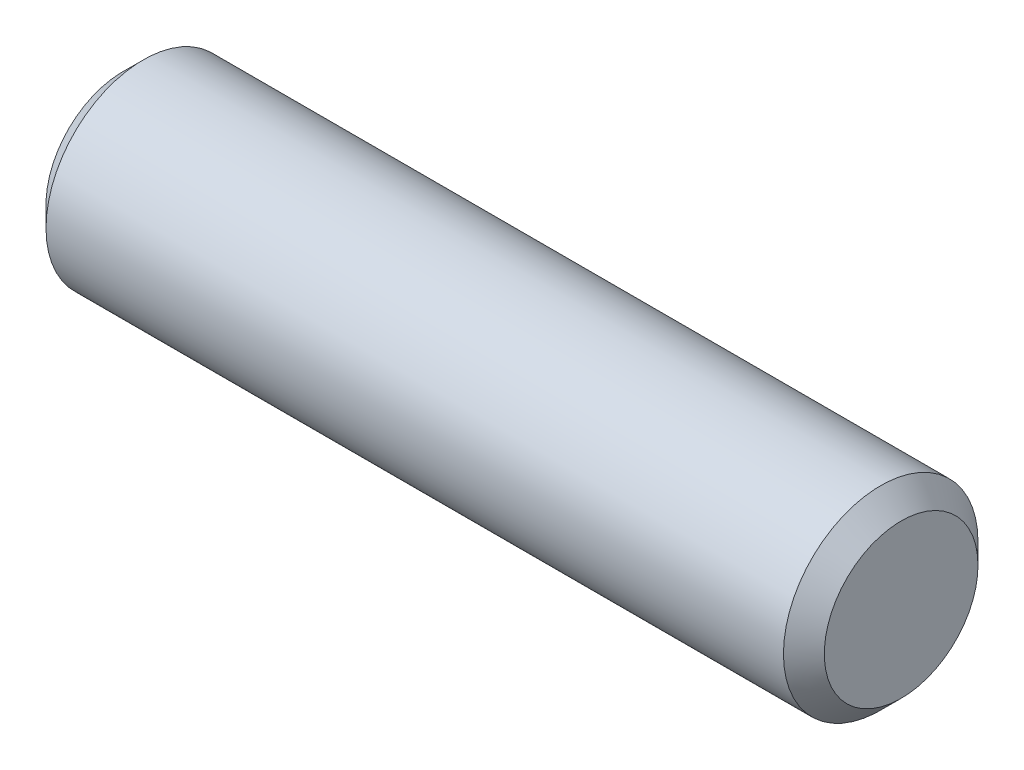
SolidWorks part; units mm, degrees
material "Brass"
ref_plane "Front Plane" through (0, 0, 0) normal (0, 0, 1) x (1, 0, 0)
ref_plane "Top Plane" through (0, 0, 0) normal (0, 1, 0) x (1, 0, 0)
ref_plane "Right Plane" through (0, 0, 0) normal (1, 0, 0) x (0, 0, -1)
sketch "Sketch2" plane through (0, 0, 0) normal (1, 0, 0) x (0, 0, -1)
  circle A0 centre (0, 0) radius 1.1906
  dimension "D1" = 2.3813
extrude "Boss-Extrude1" add sketch "Sketch2" along normal mid plane 9.525
chamfer "Chamfer1" distance 0.25 angle 45 2 edges at (4.7625, 0, -1.1906) (-4.7625, 0, -1.1906)
